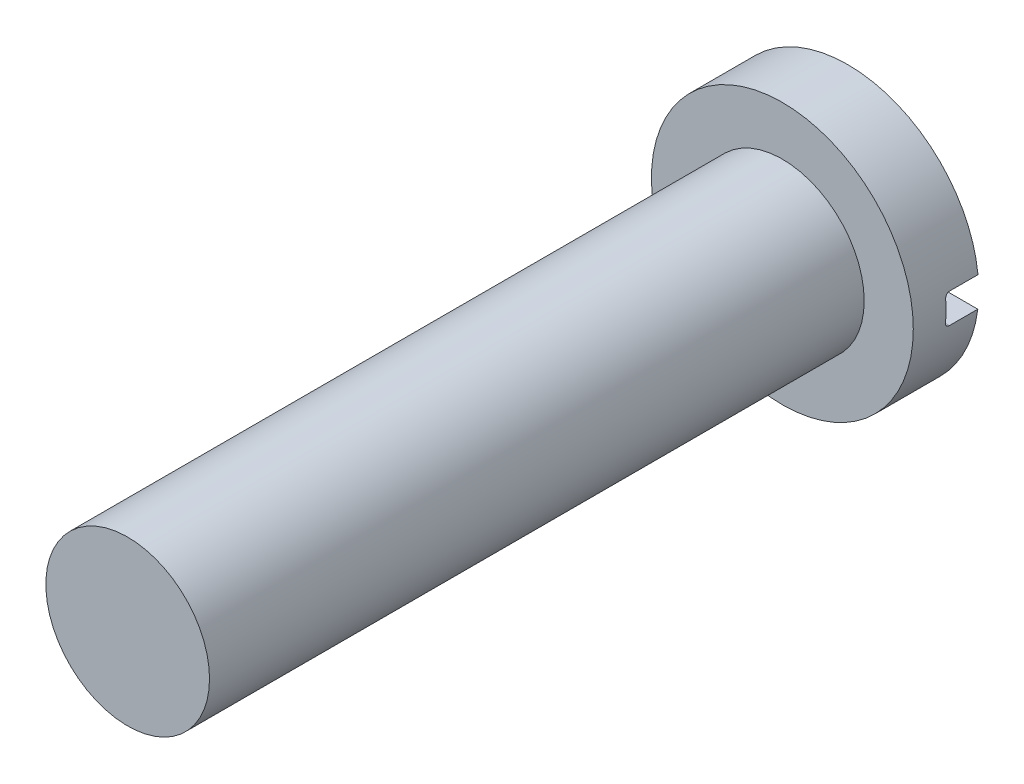
SolidWorks part; units mm, degrees
ref_plane "Front Plane" through (0, 0, 0) normal (0, 0, 1) x (1, 0, 0)
ref_plane "Top Plane" through (0, 0, 0) normal (0, 1, 0) x (1, 0, 0)
ref_plane "Right Plane" through (0, 0, 0) normal (1, 0, 0) x (0, 0, -1)
sketch "Sketch1" plane through (0, 0, 0) normal (0, 0, 1) x (1, 0, 0)
  circle A0 centre (0, 0) radius 3
  dimension "D1" = 6
extrude "Boss-Extrude1" add sketch "Sketch1" along normal blind 1.5
sketch "Sketch2" plane through (0, 0, 1.5) normal (0, 0, 1) x (1, 0, 0)
  circle A0 centre (0, 0) radius 1.875
  dimension "D1" = 3.75
extrude "Boss-Extrude2" add sketch "Sketch2" along normal blind 15
sketch "Sketch3" plane through (0, 0, 0) normal (0, 0, -1) x (-1, 0, 0)
  line L1 (-2.9826, 0.3228) -> (2.9778, 0.3228)
  line L2 (-2.9826, -0.3228) -> (-2.9826, -0.364)
  line L3 (-2.9826, -0.364) -> (2.9778, -0.364)
  line L5 (2.9778, 0.3228) -> (3.4248, 0.3228)
  line L7 (2.9778, -0.364) -> (3.4248, -0.364)
  line L8 (3.4248, 0.3228) -> (3.4248, -0.364)
  line L9 (-2.9826, 0.3228) -> (-3.4973, 0.3228)
  line L10 (-2.9826, -0.3228) -> (-2.9826, -0.364)
  line L11 (-2.9826, -0.364) -> (-3.4973, -0.364)
  line L12 (-3.4973, 0.3228) -> (-3.4973, -0.364)
  circle A0 centre (0, 0) radius 3 construction
  arc A1 (-2.9826, -0.3228) -> (-2.9778, -0.364) centre (0, 0) ccw
  circle M13 centre (0, 0) radius 3
extrude "Cut-Extrude1" cut sketch "Sketch3" against normal blind 0.75 contours L5 L1 L3 M13
fillet "Fillet2" radius 0.1 2 edges at (0, 0.3228, 0.75) (0, -0.364, 0.75)
